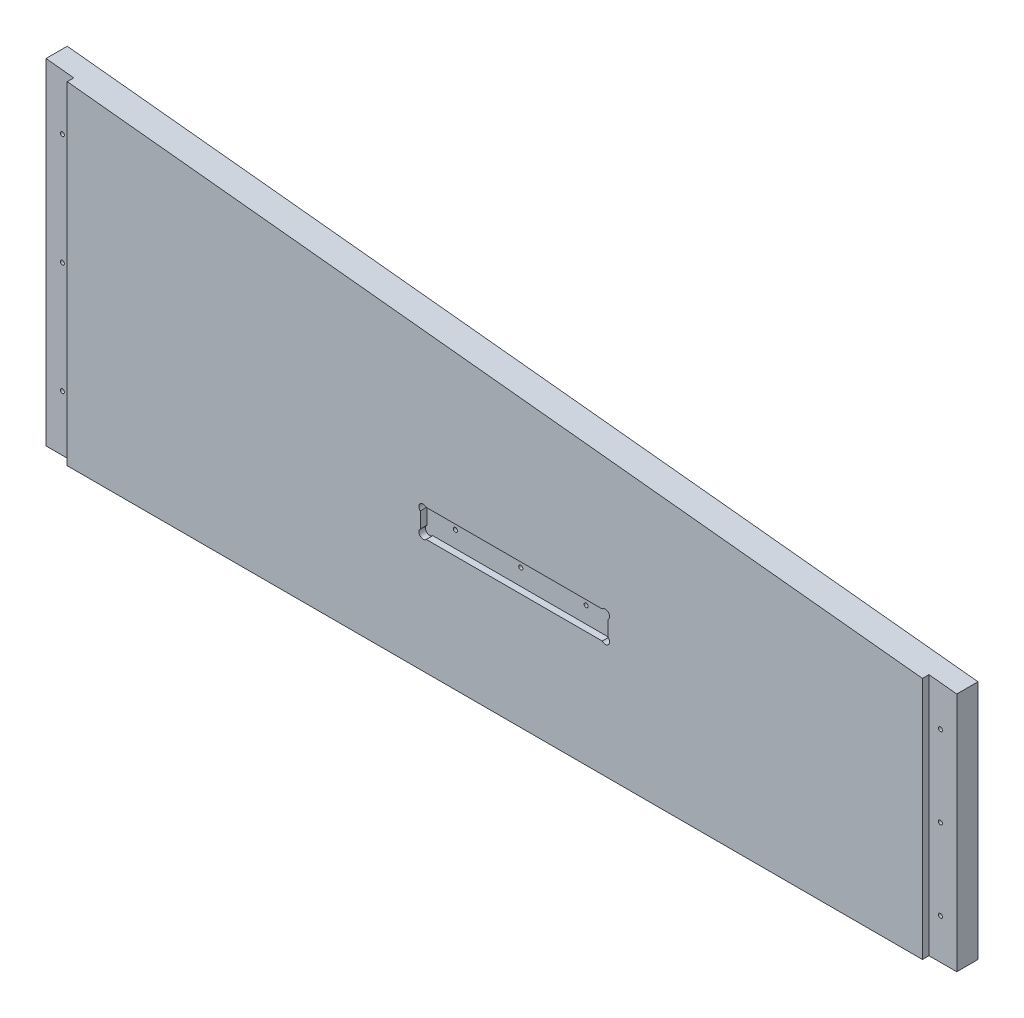
SolidWorks part; units mm, degrees
material "Pine"
ref_plane "Front Plane" through (0, 0, 0) normal (0, 0, 1) x (1, 0, 0)
ref_plane "Top Plane" through (0, 0, 0) normal (0, 1, 0) x (1, 0, 0)
ref_plane "Right Plane" through (0, 0, 0) normal (1, 0, 0) x (0, 0, -1)
sketch "Sketch1" plane through (0, 0, 0) normal (0, 0, 1) x (1, 0, 0)
  line L0 (-163.9887, -5335.905) -> (-163.9887, -5432.425)
  line L1 (-102.87, -5350.891) -> (-33.02, -5350.891)
  line L2 (-111.8235, -5341.9375) -> (-111.8235, -5334)
  line L3 (-24.0665, -5341.9375) -> (-24.0665, -5334)
  line L4 (-298.9262, -5332.73) -> (-167.1637, -5332.73)
  line L5 (-167.1637, -5435.6) -> (-298.9262, -5435.6)
  line L6 (-302.1012, -5432.425) -> (-302.1012, -5335.905)
  line L7 (-107.6325, -5329.809) -> (-28.2575, -5329.809)
  line L8 (174.9425, -5308.6) -> (174.9425, -5581.65)
  line L9 (449.2625, -5413.1661) -> (449.2625, -5421.9659)
  line L10 (595.3125, -5421.9659) -> (595.3125, -5413.1661)
  line L11 (839.47, -5509.5521) -> (839.47, -5307.6729)
  line L12 (839.47, -5307.6729) -> (863.6, -5307.6729)
  line L13 (839.47, -5509.5521) -> (863.6, -5509.5521)
  line L14 (863.6, -5509.5521) -> (863.6, -5307.6729)
  line L15 (-354.2665, -5341.9375) -> (-354.2665, -5334)
  line L16 (-100.8856, -5889.625) -> (-50.0856, -5889.625)
  line L17 (-104.0606, -5969) -> (-104.0606, -5892.8)
  line L18 (-46.9106, -5892.8) -> (-46.9106, -5969)
  line L19 (-50.0856, -5972.175) -> (-100.8856, -5972.175)
  line L20 (-100.8856, -5848.35) -> (-50.0856, -5848.35)
  line L21 (857.25, -5502.275) -> (157.1625, -5575.3)
  line L22 (857.25, -5314.95) -> (857.25, -5502.275)
  line L23 (157.1625, -5314.95) -> (157.1625, -5575.3)
  line L24 (857.25, -5314.95) -> (157.1625, -5314.95)
  line L25 (150.8125, -5308.6) -> (174.9425, -5308.6)
  line L26 (174.9425, -5581.65) -> (150.8125, -5581.65)
  line L27 (137.16, -5314.95) -> (137.16, -5502.275)
  line L28 (150.8125, -5581.65) -> (150.8125, -5308.6)
  line L29 (590.8224, -5408.676) -> (453.7526, -5408.676)
  line L30 (453.7526, -5426.456) -> (590.8224, -5426.456)
  line L31 (137.16, -6013.45) -> (137.16, -5867.4)
  line L32 (150.8125, -5746.75) -> (150.8125, -6019.8)
  line L33 (143.51, -5639.9938) -> (143.51, -5654.294)
  line L34 (590.8224, -5919.724) -> (453.7526, -5919.724)
  line L35 (453.7526, -5901.944) -> (590.8224, -5901.944)
  line L36 (449.2625, -5915.2339) -> (449.2625, -5906.4341)
  line L37 (174.9425, -6019.8) -> (174.9425, -5746.75)
  line L38 (595.3125, -5906.4341) -> (595.3125, -5915.2339)
  line L39 (839.47, -5818.8479) -> (839.47, -6020.7271)
  line L40 (839.47, -5818.8479) -> (863.6, -5818.8479)
  line L41 (863.6, -5818.8479) -> (863.6, -6020.7271)
  line L42 (839.47, -6020.7271) -> (863.6, -6020.7271)
  line L43 (-155.8782, -5867.4) -> (-603.25, -5867.4)
  line L44 (-433.07, -5350.891) -> (-363.22, -5350.891)
  line L45 (-437.8325, -5329.809) -> (-358.4575, -5329.809)
  line L46 (889, -6045.2) -> (-635, -6045.2)
  line L47 (-635, -5283.2) -> (889, -5283.2)
  line L48 (-635, -6045.2) -> (-635, -5283.2)
  line L49 (889, -5283.2) -> (889, -6045.2)
  line L50 (137.16, -5502.275) -> (-603.25, -5502.275)
  line L51 (-603.25, -5314.95) -> (137.16, -5314.95)
  line L52 (143.51, -5654.294) -> (-609.6, -5654.294)
  line L53 (-609.6, -5639.9938) -> (143.51, -5639.9938)
  line L54 (137.16, -5536.0062) -> (-603.25, -5536.0062)
  line L55 (-603.25, -5794.375) -> (137.16, -5794.375)
  line L56 (-603.25, -6013.45) -> (137.16, -6013.45)
  line L57 (-603.25, -5536.0062) -> (-603.25, -5794.375)
  line L58 (137.16, -5794.375) -> (137.16, -5536.0062)
  line L59 (-609.6, -5654.294) -> (-609.6, -5639.9938)
  line L60 (-603.25, -5867.4) -> (-603.25, -6013.45)
  line L61 (-603.25, -5314.95) -> (-603.25, -5502.275)
  line L62 (-442.0235, -5341.9375) -> (-442.0235, -5334)
  line L63 (857.25, -5826.125) -> (157.1625, -5753.1)
  line L64 (857.25, -6013.45) -> (857.25, -5826.125)
  line L65 (157.1625, -6013.45) -> (157.1625, -5753.1)
  line L66 (857.25, -6013.45) -> (157.1625, -6013.45)
  line L67 (174.9425, -5746.75) -> (150.8125, -5746.75)
  line L68 (150.8125, -6019.8) -> (174.9425, -6019.8)
  line L69 (137.16, -5867.4) -> (4.907, -5867.4)
  circle A0 centre (-36.195, -5484.0124) radius 1.5875
  arc A1 (-298.9262, -5332.73) -> (-302.1012, -5335.905) centre (-298.9262, -5335.905) ccw
  arc A2 (-302.1012, -5432.425) -> (-298.9262, -5435.6) centre (-298.9262, -5432.425) ccw
  arc A3 (-163.9887, -5335.905) -> (-167.1637, -5332.73) centre (-167.1637, -5335.905) ccw
  arc A4 (-167.1637, -5435.6) -> (-163.9887, -5432.425) centre (-167.1637, -5432.425) ccw
  arc A5 (-111.8235, -5341.9375) -> (-102.87, -5350.891) centre (-102.87, -5341.9375) ccw
  arc A6 (-107.6325, -5329.809) -> (-111.8235, -5334) centre (-107.6325, -5334) ccw
  circle A7 centre (166.0525, -5444.6613) radius 1.5875
  circle A8 centre (166.0525, -5358.1871) radius 1.5875
  circle A9 centre (471.4875, -5417.566) radius 1.5875
  arc A10 (453.7526, -5408.676) -> (449.2625, -5413.1661) centre (451.5076, -5410.9211) ccw
  arc A11 (449.2625, -5421.9659) -> (453.7526, -5426.456) centre (451.5076, -5424.2109) ccw
  circle A12 centre (522.2875, -5417.566) radius 1.5875
  circle A13 centre (573.0875, -5417.566) radius 1.5875
  arc A14 (590.8224, -5426.456) -> (595.3125, -5421.9659) centre (593.0674, -5424.2109) ccw
  arc A15 (595.3125, -5413.1661) -> (590.8224, -5408.676) centre (593.0674, -5410.9211) ccw
  circle A16 centre (848.36, -5471.8269) radius 1.5875
  circle A17 centre (848.36, -5409.0762) radius 1.5875
  circle A18 centre (848.36, -5346.3254) radius 1.5875
  arc A19 (-363.22, -5350.891) -> (-354.2665, -5341.9375) centre (-363.22, -5341.9375) ccw
  arc A20 (-354.2665, -5334) -> (-358.4575, -5329.809) centre (-358.4575, -5334) ccw
  arc A21 (-24.0665, -5334) -> (-28.2575, -5329.809) centre (-28.2575, -5334) ccw
  arc A22 (-33.02, -5350.891) -> (-24.0665, -5341.9375) centre (-33.02, -5341.9375) ccw
  circle A23 centre (-86.995, -5484.0124) radius 1.5875
  circle A24 centre (-333.4544, -5894.07) radius 2.54
  circle A25 centre (-333.4544, -5994.4) radius 2.54
  arc A26 (-104.0606, -5969) -> (-100.8856, -5972.175) centre (-100.8856, -5969) ccw
  arc A27 (-50.0856, -5972.175) -> (-46.9106, -5969) centre (-50.0856, -5969) ccw
  arc A28 (-100.8856, -5848.35) -> (-128.3819, -5857.875) centre (-100.8856, -5892.8) ccw
  arc A29 (-155.8782, -5867.4) -> (-128.3819, -5857.875) centre (-155.8782, -5822.95) ccw
  arc A30 (-22.5893, -5857.875) -> (-50.0856, -5848.35) centre (-50.0856, -5892.8) ccw
  circle A31 centre (-132.6356, -5894.07) radius 2.54
  circle A32 centre (-132.6356, -5994.4) radius 2.54
  arc A33 (-46.9106, -5892.8) -> (-50.0856, -5889.625) centre (-50.0856, -5892.8) ccw
  arc A34 (-100.8856, -5889.625) -> (-104.0606, -5892.8) centre (-100.8856, -5892.8) ccw
  arc A35 (-22.5893, -5857.875) -> (4.907, -5867.4) centre (4.907, -5822.95) ccw
  circle A36 centre (166.0525, -5531.1356) radius 1.5875
  arc A37 (449.2625, -5915.2339) -> (453.7526, -5919.724) centre (451.5076, -5917.4789) ccw
  arc A38 (453.7526, -5901.944) -> (449.2625, -5906.4341) centre (451.5076, -5904.1891) ccw
  circle A39 centre (166.0525, -5797.2644) radius 1.5875
  circle A40 centre (166.0525, -5883.7387) radius 1.5875
  circle A41 centre (166.0525, -5970.2129) radius 1.5875
  circle A42 centre (471.4875, -5910.834) radius 1.5875
  circle A43 centre (522.2875, -5910.834) radius 1.5875
  circle A44 centre (573.0875, -5910.834) radius 1.5875
  arc A45 (595.3125, -5906.4341) -> (590.8224, -5901.944) centre (593.0674, -5904.1891) ccw
  arc A46 (590.8224, -5919.724) -> (595.3125, -5915.2339) centre (593.0674, -5917.4789) ccw
  circle A47 centre (848.36, -5919.3238) radius 1.5875
  circle A48 centre (848.36, -5982.0746) radius 1.5875
  circle A49 centre (848.36, -5856.5731) radius 1.5875
  arc A50 (-437.8325, -5329.809) -> (-442.0235, -5334) centre (-437.8325, -5334) ccw
  circle A51 centre (-429.895, -5484.0124) radius 1.5875
  arc A52 (-442.0235, -5341.9375) -> (-433.07, -5350.891) centre (-433.07, -5341.9375) ccw
  circle A53 centre (-379.095, -5484.0124) radius 1.5875
sketch "HeadSideRightOutline" plane through (0, 0, 0) normal (0, 0, 1) x (1, 0, 0)
  line L0 (174.9425, -6013.45) -> (839.47, -6013.45)
  line L1 (839.47, -6013.45) -> (839.47, -5824.2704)
  line L2 (839.47, -5824.2704) -> (174.9425, -5754.9546)
  line L3 (174.9425, -5754.9546) -> (174.9425, -6013.45)
extrude "HeadSideRight_Thickness" add sketch "HeadSideRightOutline" against normal blind 21.59
sketch "Sketch10" plane through (0, 0, -21.59) normal (0, 0, -1) x (-1, 0, 0)
  line L0 (-174.9425, -6013.45) -> (-153.3525, -6013.45)
  line L1 (-153.3525, -6013.45) -> (-153.3525, -5752.7026)
  line L2 (-153.3525, -5752.7026) -> (-174.9425, -5754.9546)
  line L3 (-174.9425, -5754.9546) -> (-174.9425, -6013.45)
  line L4 (-839.47, -6013.45) -> (-861.06, -6013.45)
  line L5 (-861.06, -6013.45) -> (-861.06, -5826.5224)
  line L6 (-861.06, -5826.5224) -> (-839.47, -5824.2704)
  line L7 (-839.47, -5824.2704) -> (-839.47, -6013.45)
  line L8 (-857.25, -5826.125) -> (-157.1625, -5753.1) construction
  dimension "D1" = 21.59
  dimension "D2" = 21.59
extrude "Extrude4" add sketch "Sketch10" against normal blind 16.51
sketch "Sketch8" plane through (0, 0, 0) normal (0, 0, 1) x (1, 0, 0)
  circle A0 centre (166.0525, -5970.2129) radius 1.5875
  circle A1 centre (166.0525, -5883.7387) radius 1.5875
  circle A2 centre (166.0525, -5797.2644) radius 1.5875
  circle A3 centre (848.36, -5982.0746) radius 1.5875
  circle A4 centre (848.36, -5919.3238) radius 1.5875
  circle A5 centre (848.36, -5856.5731) radius 1.5875
  circle A6 centre (471.4875, -5910.834) radius 1.5875
  circle A7 centre (522.2875, -5910.834) radius 1.5875
  circle A8 centre (573.0875, -5910.834) radius 1.5875
extrude "Cut-Extrude4" cut sketch "Sketch8" against normal up to surface (21.59 mm away) up to face at (507.2062, -5901.5312, -21.59)
sketch "Sketch9" plane through (0, 0, 0) normal (0, 0, 1) x (1, 0, 0)
  line L12 (449.2625, -5923.534) -> (595.3125, -5923.534)
  line L13 (449.2625, -5901.944) -> (595.3125, -5901.944)
  line L14 (449.2625, -5901.944) -> (449.2625, -5923.534)
  line L15 (595.3125, -5901.944) -> (595.3125, -5923.534)
  dimension "D1" = 21.59
extrude "Cut-Extrude5" cut sketch "Sketch9" against normal blind 5.08
sketch "Sketch11" plane through (0, 0, 0) normal (0, 0, 1) x (1, 0, 0)
  line L0 (595.3125, -5901.944) -> (593.0674, -5904.1891) construction
  line L1 (595.3125, -5923.534) -> (593.0674, -5921.2889) construction
  line L2 (449.2625, -5923.534) -> (451.5076, -5921.2889) construction
  line L3 (449.2625, -5901.944) -> (451.5076, -5904.1891) construction
  line L4 (449.2625, -5923.534) -> (595.3125, -5923.534) construction
  line L5 (595.3125, -5901.944) -> (449.2625, -5901.944) construction
  line L6 (449.2625, -5923.534) -> (595.3125, -5923.534) construction
  line L7 (595.3125, -5901.944) -> (449.2625, -5901.944) construction
  circle A0 centre (451.5076, -5904.1891) radius 3.302
  circle A1 centre (451.5076, -5921.2889) radius 3.302
  circle A2 centre (593.0674, -5921.2889) radius 3.302
  circle A3 centre (593.0674, -5904.1891) radius 3.302
  dimension "D1" = 45
  dimension "D2" = 45
  dimension "D3" = 3.175
  dimension "D4" = 3.175
  dimension "D5" = 45
  dimension "D6" = 45
  dimension "D7" = 3.175
  dimension "D8" = 3.175
extrude "Cut-Extrude6" cut sketch "Sketch11" against normal up to surface (5.08 mm away) up to face at (523.875, -5910.834, -5.08)
